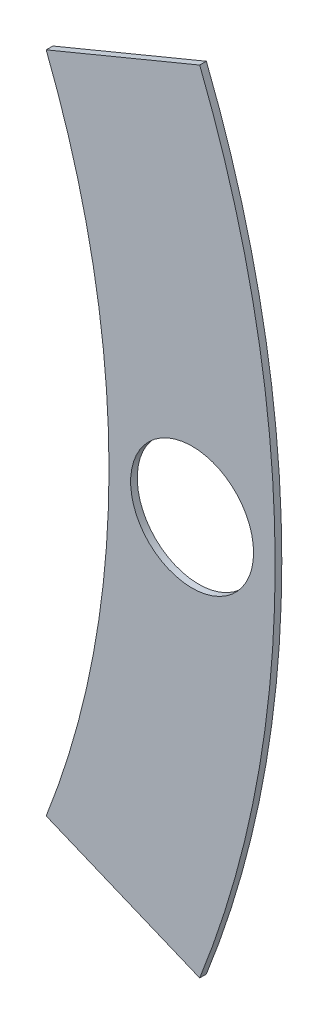
SolidWorks part; units mm, degrees
material "Copper"
ref_plane "Front Plane" through (0, 0, 0) normal (0, 0, 1) x (1, 0, 0)
ref_plane "Top Plane" through (0, 0, 0) normal (0, 1, 0) x (1, 0, 0)
ref_plane "Right Plane" through (0, 0, 0) normal (1, 0, 0) x (0, 0, -1)
sketch "Sketch4" plane through (0, 0, 0) normal (0, 0, 1) x (1, 0, 0)
  circle A0 centre (0, 0) radius 82.042
  dimension "D1" = 164.084
extrude "Boss-Extrude2" add sketch "Sketch4" along normal blind 0.508
sketch "Sketch5" plane through (0, 0, 0.508) normal (0, 0, 1) x (1, 0, 0)
  circle A0 centre (0, 0) radius 69.342
  circle A1 centre (0, 0) radius 82.042 construction
  dimension "D1" = 12.7
extrude "Cut-Extrude5" cut sketch "Sketch5" against normal through all
sketch "Sketch6" plane through (0, 0, 0.508) normal (0, 0, 1) x (1, 0, 0)
  line L0 (0, 0) -> (75.692, 0) construction
  circle A0 centre (75.692, 0) radius 4.699
  circle A1 centre (0, 0) radius 69.342 construction
  dimension "D2" = 9.398
  dimension "D1" = 6.35
extrude "Cut-Extrude6" cut sketch "Sketch6" against normal through all
sketch "Sketch8" plane through (0, 0, 0.508) normal (0, 0, 1) x (1, 0, 0)
  line L0 (0, 0) -> (75.7969, 31.3961) construction
  line L1 (0, 0) -> (75.7969, -31.3961) construction
  line L2 (64.5389, -25.3583) -> (76.2739, -30.219)
  line L3 (64.5389, 25.3583) -> (76.2739, 30.219)
  line L6 (0, 0) -> (101.6, 0) construction
  circle A0 centre (0, 0) radius 82.042 construction
  arc A1 (76.2739, -30.219) -> (76.2739, 30.219) centre (0, 0) ccw
  arc A3 (64.5389, -25.3583) -> (64.5389, 25.3583) centre (0, 0) ccw
  circle A4 centre (0, 0) radius 69.342 construction
  point P26 (0, 0)
  dimension "D3" = 1.27
  dimension "D4" = 1.27
  dimension "D1" = 22.5
  dimension "D2" = 22.5
  dimension "D5" = 1.27
  dimension "D6" = 1.27
extrude "Cut-Extrude11" cut sketch "Sketch8" against normal through all flip side to cut
